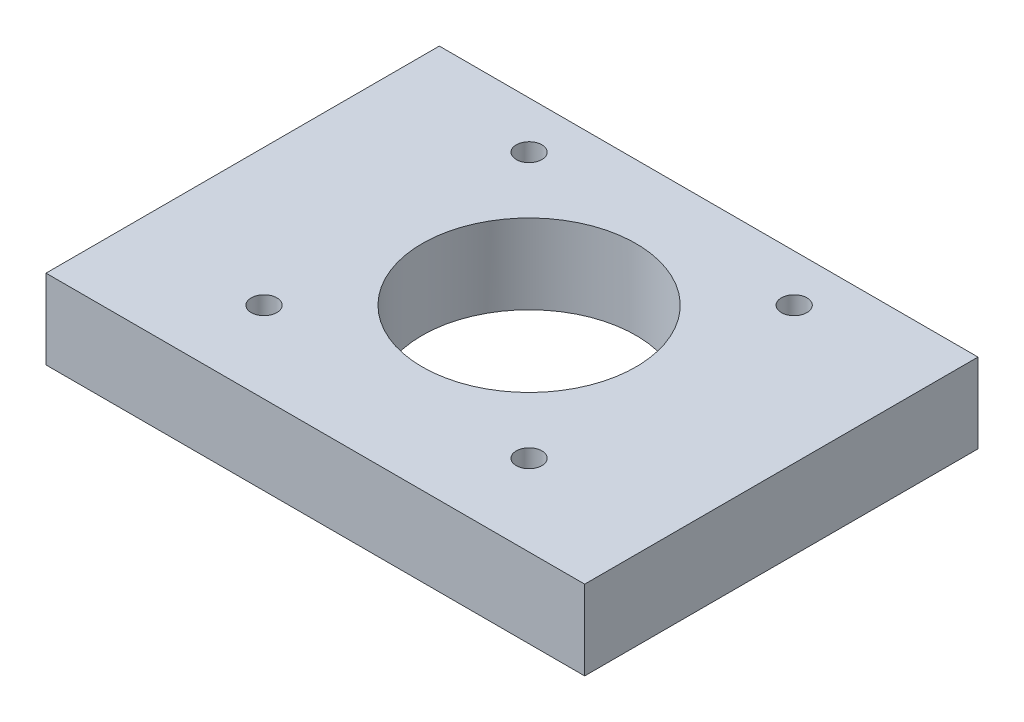
SolidWorks part; units mm, degrees
ref_plane "Front Plane" through (0, 0, 0) normal (0, 0, 1) x (1, 0, 0)
ref_plane "Top Plane" through (0, 0, 0) normal (0, 1, 0) x (1, 0, 0)
ref_plane "Right Plane" through (0, 0, 0) normal (1, 0, 0) x (0, 0, -1)
sketch "Sketch1" plane through (0, 0, 0) normal (0, 0, 1) x (1, 0, 0)
  line L0 (0, 0) -> (-31.5, 0)
  line L1 (-31.5, 0) -> (-31.5, 9.3)
  line L2 (-31.5, 9.3) -> (31.5, 9.3)
  line L3 (31.5, 9.3) -> (31.5, 0)
  line L4 (31.5, 0) -> (0, 0)
  line L5 (-21.5, 9.3) -> (-21.5, 0) construction
  line L6 (0, 0) -> (0, 9.3) construction
  line L7 (21.5, 9.3) -> (21.5, 0) construction
  dimension "D1" = 10
  dimension "D2" = 9.3
  dimension "D3" = 10
  dimension "D4" = 43
extrude "Boss-Extrude1" add sketch "Sketch1" along normal blind 46
sketch "Sketch2" plane through (0, 9.3, 0) normal (0, 1, 0) x (1, 0, 0)
  line L0 (0, 0) -> (0, -46) construction
  line L1 (31.5, 0) -> (-31.5, 0) construction
  line L2 (31.5, -46) -> (-31.5, -46) construction
  line L3 (0, -21) -> (-31.5, -21) construction
  line L4 (-31.5, -46) -> (-31.5, 0) construction
  circle A0 centre (0, -21) radius 12.5
  circle A1 centre (-15.5, -5.5) radius 1.5
  circle A2 centre (-15.5, -36.5) radius 1.5
  circle A3 centre (15.5, -5.5) radius 1.5
  circle A4 centre (15.5, -36.5) radius 1.5
  dimension "D1" = 25
  dimension "D3" = 3
  dimension "D2" = 25
  dimension "D4" = 15.5
  dimension "D5" = 15.5
extrude "Cut-Extrude1" cut sketch "Sketch2" against normal up to next
